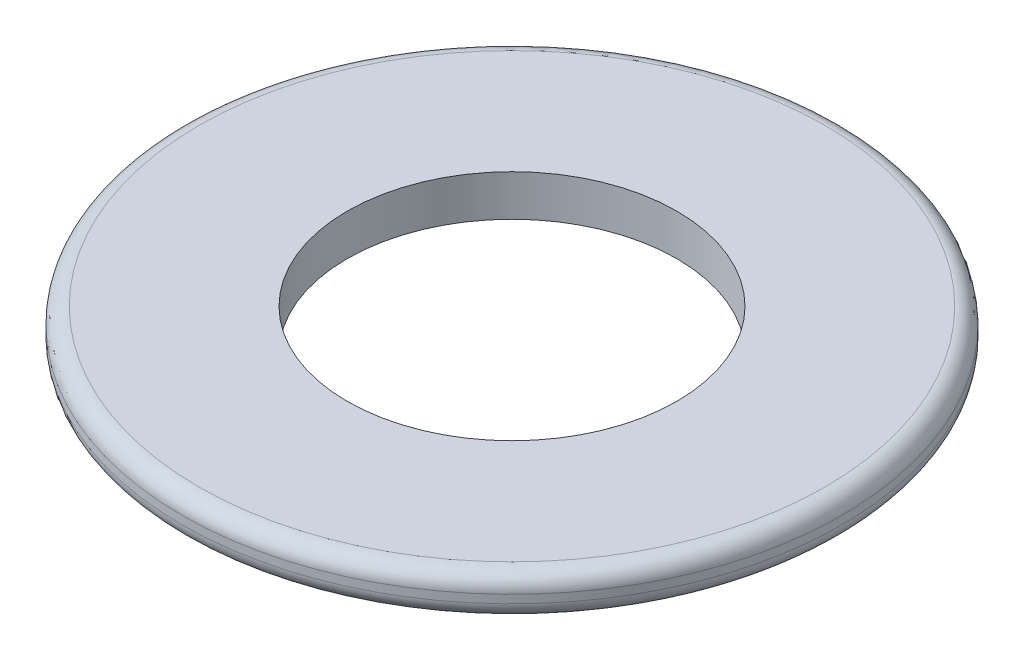
SolidWorks part; units mm, degrees
ref_plane "Front Plane" through (0, 0, 0) normal (0, 0, 1) x (1, 0, 0)
ref_plane "Top Plane" through (0, 0, 0) normal (0, 1, 0) x (1, 0, 0)
ref_plane "Right Plane" through (0, 0, 0) normal (1, 0, 0) x (0, 0, -1)
sketch "Sketch1" plane through (0, 0, 0) normal (0, 1, 0) x (1, 0, 0)
  circle A0 centre (0, 0) radius 2
  circle A1 centre (0, 0) radius 4
  dimension "D1" = 4
  dimension "D2" = 8
extrude "Boss-Extrude1" add sketch "Sketch1" along normal blind 0.5
fillet "Fillet1" radius 0.2 1 edges at (0, 0.5, 4)
fillet "Fillet2" radius 0.2 1 edges at (0, 0, 4)
